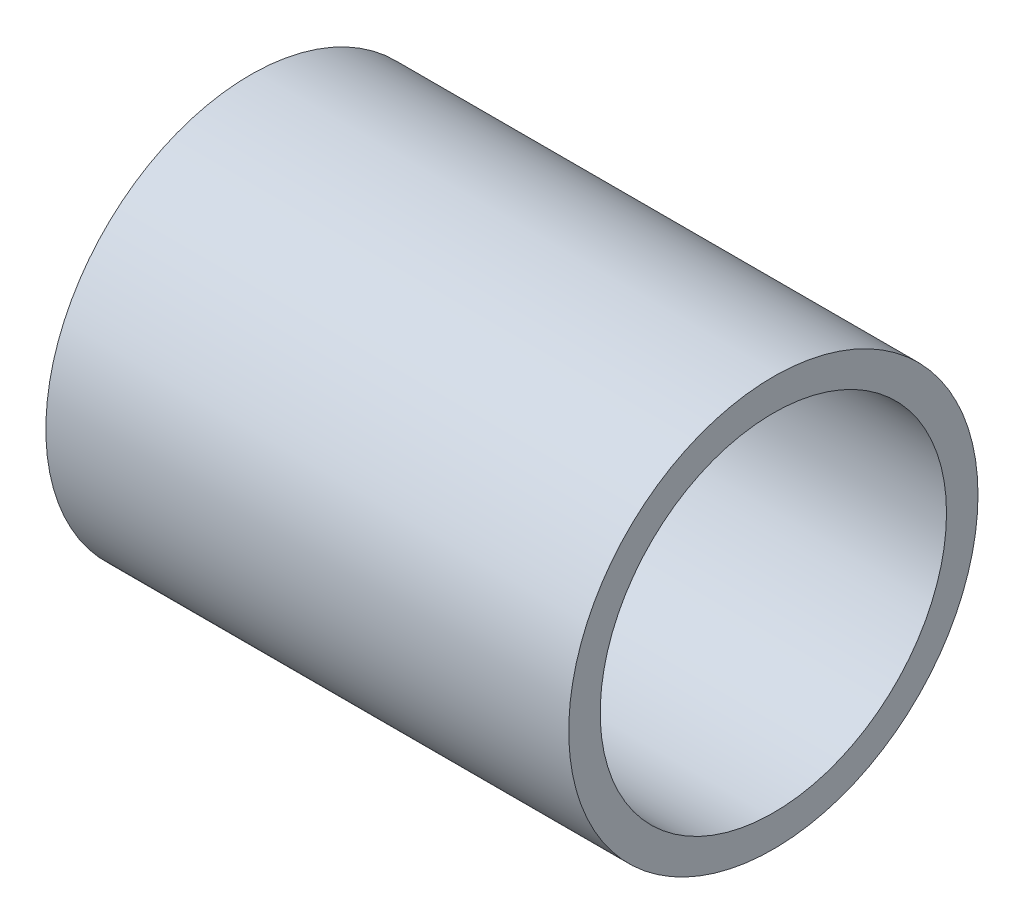
SolidWorks part; units mm, degrees
material "Nylon 101"
ref_plane "Front Plane" through (0, 0, 0) normal (0, 0, 1) x (1, 0, 0)
ref_plane "Top Plane" through (0, 0, 0) normal (0, 1, 0) x (1, 0, 0)
ref_plane "Right Plane" through (0, 0, 0) normal (1, 0, 0) x (0, 0, -1)
sketch "Sketch1" plane through (0, 0, 0) normal (1, 0, 0) x (0, 0, -1)
  circle A0 centre (0, 0) radius 32.5
  circle A1 centre (0, 0) radius 27.5
  dimension "D1" = 65
  dimension "D2" = 55
extrude "Boss-Extrude1" add sketch "Sketch1" along normal blind 83.04
